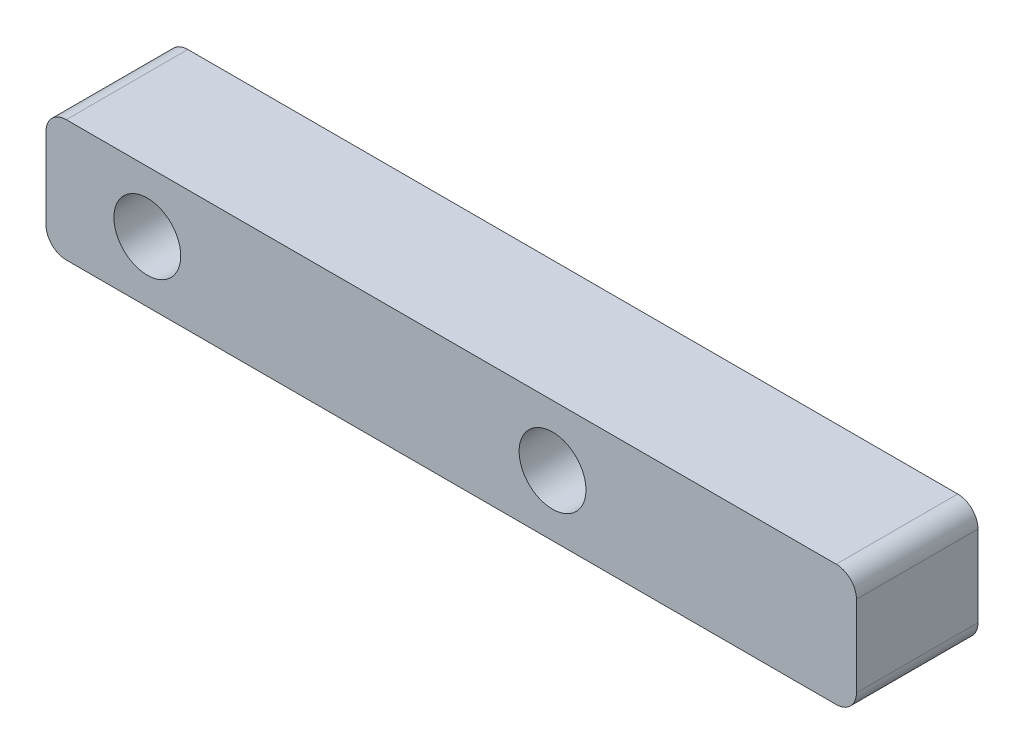
SolidWorks part; units mm, degrees
material "ABS"
ref_plane "前视基准面" through (0, 0, 0) normal (0, 0, 1) x (1, 0, 0)
ref_plane "上视基准面" through (0, 0, 0) normal (0, 1, 0) x (1, 0, 0)
ref_plane "右视基准面" through (0, 0, 0) normal (1, 0, 0) x (0, 0, -1)
other "Configuration Table"
sketch "草图1" plane through (0, 0, 0) normal (0, 0, 1) x (1, 0, 0)
  line L1 (-20, -3) -> (20, -3)
  line L2 (-20, -3) -> (-20, 3)
  line L3 (-20, 3) -> (20, 3)
  line L4 (20, -3) -> (20, 3)
  line L5 (-20, -3) -> (20, 3) construction
  line L6 (-20, 3) -> (20, -3) construction
  point P0 (0, 0)
  dimension "D1" = 40
  dimension "D2" = 6
extrude "凸台-拉伸1" add sketch "草图1" along normal blind 6
sketch "草图2" plane through (0, 0, 6) normal (0, 0, 1) x (1, 0, 0)
  line L0 (-20, 3) -> (-20, -3) construction
  circle A0 centre (5, 0) radius 1.65
  circle A1 centre (-15, 0) radius 1.65
  dimension "D1" = 3.3
  dimension "D3" = 5
  dimension "D2" = 20
extrude "切除-拉伸1" cut sketch "草图2" against normal blind 6
fillet "圆角1" radius 1 4 edges at (20, -3, 3) (-20, -3, 3) (20, 3, 3) (-20, 3, 3)
